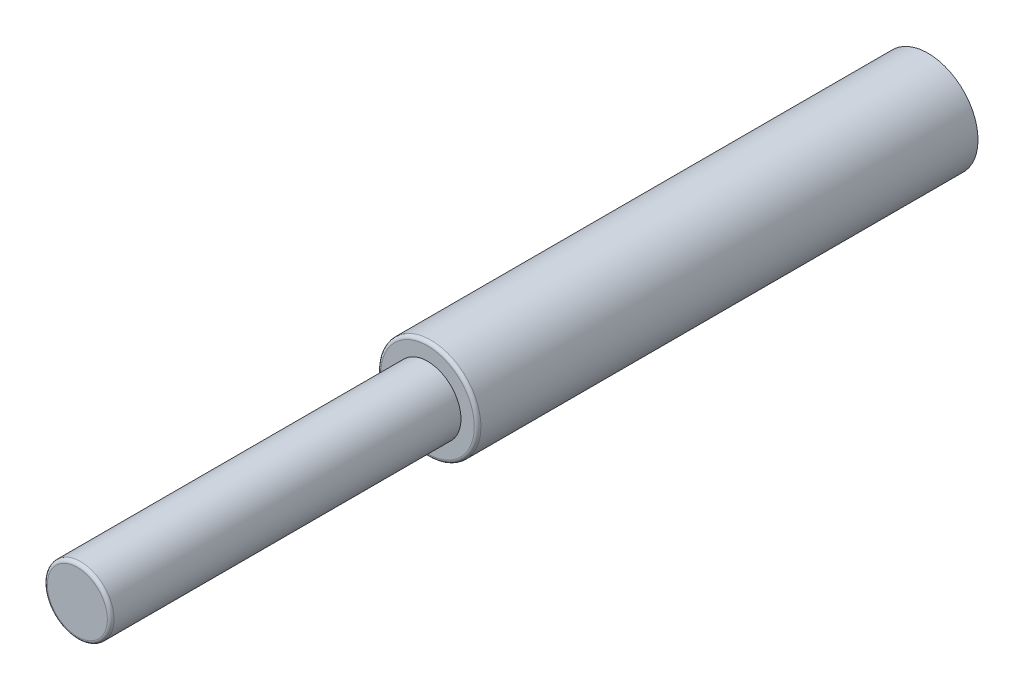
SolidWorks part; units mm, degrees
ref_plane "Front Plane" through (0, 0, 0) normal (0, 0, 1) x (1, 0, 0)
ref_plane "Top Plane" through (0, 0, 0) normal (0, 1, 0) x (1, 0, 0)
ref_plane "Right Plane" through (0, 0, 0) normal (1, 0, 0) x (0, 0, -1)
sketch "Sketch2" plane through (0, 0, 0) normal (0, 0, 1) x (1, 0, 0)
  circle A0 centre (0, 0) radius 30
  dimension "D1" = 60
extrude "Boss-Extrude1" add sketch "Sketch2" along normal blind 300
sketch "Sketch3" plane through (0, 0, 300) normal (0, 0, 1) x (1, 0, 0)
  circle A0 centre (0, 0) radius 20
  dimension "D1" = 40
extrude "Boss-Extrude2" add sketch "Sketch3" along normal blind 210
fillet "Fillet1" radius 2 1 edges at (20, 0, 510)
fillet "Fillet2" radius 2 1 edges at (30, 0, 300)
